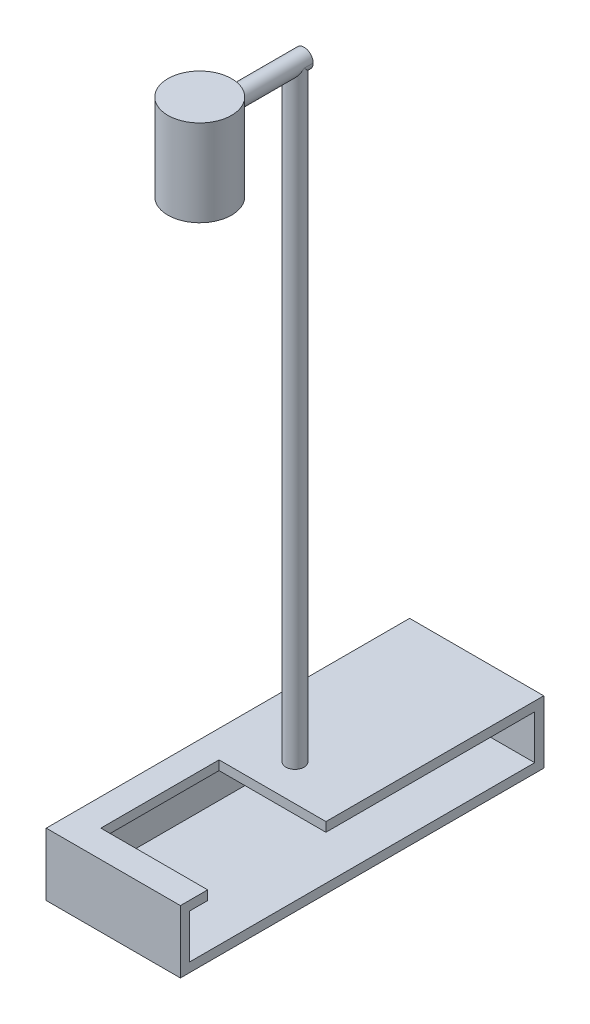
SolidWorks part; units mm, degrees
ref_plane "Front Plane" through (0, 0, 0) normal (0, 0, 1) x (1, 0, 0)
ref_plane "Top Plane" through (0, 0, 0) normal (0, 1, 0) x (1, 0, 0)
ref_plane "Right Plane" through (0, 0, 0) normal (1, 0, 0) x (0, 0, -1)
sketch "Sketch1" plane through (0, 0, 0) normal (0, 0, 1) x (1, 0, 0)
  line L1 (-14.75, -6.895) -> (14.75, -6.895)
  line L2 (-14.75, -6.895) -> (-14.75, 6.895)
  line L3 (-14.75, 6.895) -> (14.75, 6.895)
  line L4 (14.75, -6.895) -> (14.75, 6.895)
  line L5 (-14.75, -6.895) -> (14.75, 6.895) construction
  line L6 (-14.75, 6.895) -> (14.75, -6.895) construction
  point P0 (0, 0)
  dimension "D1" = 29.5
  dimension "D2" = 13.79
sketch "Sketch3" plane through (0, 0, 0) normal (0, 1, 0) x (1, 0, 0)
  circle A0 centre (0, -39.95) radius 2.5
  dimension "D2" = 5
  dimension "D1" = 39.95
sketch "Sketch4" plane through (0, 0, 0) normal (0, 1, 0) x (1, 0, 0)
  circle A0 centre (0, -39.95) radius 2
  dimension "D1" = 4
  dimension "D2" = 0
extrude "Boss-Extrude1" add sketch "Sketch4" along normal blind 140 contours A0
sketch "Sketch5" plane through (0, 0, 0) normal (0, 0, 1) x (1, 0, 0)
  line L0 (-14.75, -6.895) -> (14.75, -6.895)
  line L1 (-14.75, -6.895) -> (-14.75, 6.895)
  line L2 (-14.75, 6.895) -> (14.75, 6.895)
  line L3 (14.75, -6.895) -> (14.75, 6.895)
extrude "Boss-Extrude3" add sketch "Sketch5" along normal blind 79.9
sketch "Sketch6" plane through (14.75, 0, 0) normal (1, 0, 0) x (0, 0, -1)
  line L0 (-37.45, 0) -> (-42.45, 0) construction
  line L2 (-77.9, 4.85) -> (-2, 4.85)
  line L3 (-77.9, 4.85) -> (-77.9, -4.85)
  line L4 (-77.9, -4.85) -> (-2, -4.85)
  line L5 (-2, 4.85) -> (-2, -4.85)
  line L6 (-77.9, 4.85) -> (-2, -4.85) construction
  line L7 (-77.9, -4.85) -> (-2, 4.85) construction
  point P2 (-39.95, 0)
  dimension "D1" = 9.7
  dimension "D2" = 75.9
extrude "Cut-Extrude1" cut sketch "Sketch6" against normal blind 27.5
sketch "Sketch7" plane through (0, 6.895, 0) normal (0, 1, 0) x (1, 0, 0)
  line L0 (-14.75, -79.9) -> (-14.75, 0) construction
  line L1 (-8.75, -47.9) -> (14.75, -47.9)
  line L2 (-8.75, -47.9) -> (-8.75, -73.9)
  line L3 (-8.75, -73.9) -> (14.75, -73.9)
  line L4 (14.75, -47.9) -> (14.75, -73.9)
  line L5 (-8.75, -47.9) -> (14.75, -73.9) construction
  line L6 (-8.75, -73.9) -> (14.75, -47.9) construction
  line L7 (14.75, -79.9) -> (-14.75, -79.9) construction
  line L10 (14.75, -79.9) -> (14.75, 0) construction
  point P0 (3, -60.9)
  point P7 (-8.75, -60.9)
  dimension "D1" = 26
  dimension "D2" = 0
  dimension "D3" = 6
  dimension "D4" = 6
extrude "Cut-Extrude2" cut sketch "Sketch7" against normal blind 3 contours L2 L3 L4 L1
ref_plane "Plane3" through (0, 0, 37.95) normal (0, 0, 1) x (1, 0, 0)
sketch "Sketch8" plane through (0, 0, 37.95) normal (0, 0, 1) x (1, 0, 0)
  line L0 (2, 140) -> (-2, 140) construction
  circle A0 centre (0, 140) radius 2
extrude "Boss-Extrude4" add sketch "Sketch8" along normal blind 22.95
ref_plane "Plane4" through (0, 102, 0) normal (0, 1, 0) x (1, 0, 0)
ref_plane "Plane8" through (0, 140, 0) normal (0, 1, 0) x (1, 0, 0)
sketch "Sketch12" plane through (0, 140, 0) normal (0, 1, 0) x (1, 0, 0)
  circle A2 centre (0, -60.9) radius 7
  dimension "D1" = 14
extrude "Boss-Extrude6" add sketch "Sketch12" against normal blind 15.01
sketch "Sketch13" plane through (0, 140, 0) normal (0, 1, 0) x (1, 0, 0)
  circle A0 centre (0, -60.9) radius 7
  dimension "D1" = 14
extrude "Boss-Extrude7" add sketch "Sketch13" along normal blind 4
ref_plane "Plane7" through (14.75, -4.85, 2) normal (0, 1, 0) x (1, 0, 0)
sketch "Sketch14" plane through (0, 124.99, 0) normal (0, -1, 0) x (1, 0, 0)
  circle A0 centre (0, 60.9) radius 5.5
  dimension "D1" = 11
extrude "Cut-Extrude3" cut sketch "Sketch14" against normal blind 12
